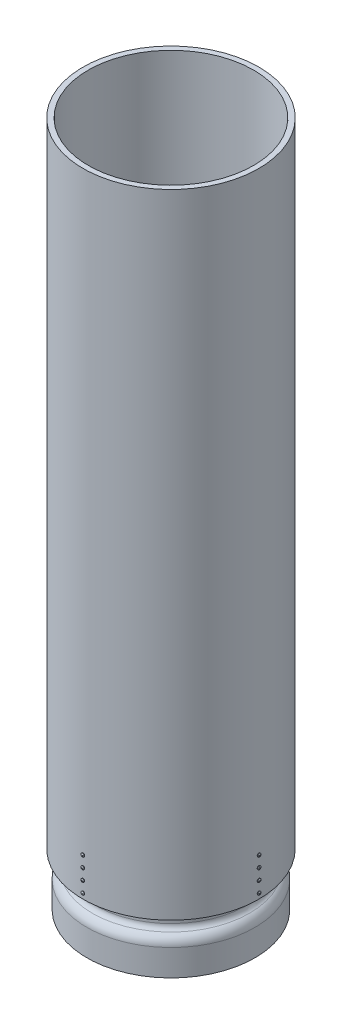
SolidWorks part; units mm, degrees
ref_plane "Front" through (0, 0, 0) normal (0, 0, 1) x (1, 0, 0)
ref_plane "Top" through (0, 0, 0) normal (0, 1, 0) x (1, 0, 0)
ref_plane "Right" through (0, 0, 0) normal (1, 0, 0) x (0, 0, -1)
sketch "Sketch2" plane through (0, 0, 0) normal (0, 0, 1) x (1, 0, 0)
  line L0 (0, -96.4651) -> (0, 112.46) construction
  line L1 (-228.6, 0) -> (-228.6, 76.2)
  line L2 (-238.9378, 152.4) -> (-238.9378, 1981.2)
  line L3 (-238.9378, 1981.2) -> (-254, 1981.2)
  line L4 (-254, 1981.2) -> (-254, 152.4)
  line L5 (-254, 152.4) -> (-238.9378, 152.4)
  line L6 (-228.6, 0) -> (-242.8748, 0)
  line L7 (-242.8748, 0) -> (-242.8748, 76.2)
  line L10 (0, 79.375) -> (0, 76.2)
  line L12 (-218.3003, 118.8009) -> (-218.3003, 279.4)
  line L13 (-218.3003, 279.4) -> (-204.0255, 279.4)
  line L14 (-204.0255, 279.4) -> (-204.0255, 118.8009)
  arc A0 (-227.0203, 103.6845) -> (-242.8748, 76.2) centre (-211.1248, 76.2) ccw
  arc A2 (-219.88, 91.3165) -> (-228.6, 76.2) centre (-211.1375, 76.2) ccw
  arc A3 (-219.88, 91.3165) -> (-204.0255, 118.8009) centre (-235.7755, 118.8009) ccw
  arc A4 (-227.0203, 103.6845) -> (-218.3003, 118.8009) centre (-235.7628, 118.8009) ccw
  dimension "D9" = 17.4625
  dimension "D10" = 76.2
  dimension "D8" = 31.75
  dimension "D13" = 31.75
  dimension "D14" = 17.4625
  dimension "D1" = 1981.2
  dimension "D2" = 14.2748
  dimension "D3" = 15.0622
  dimension "D4" = 508
  dimension "D5" = 457.2
  dimension "D6" = 152.4
  dimension "D7" = 14.2748
  dimension "D11" = 279.4
  dimension "D12" = 20.6375
revolve "Revolve1" add sketch "Sketch2" angle 360 about L0
sketch "Sketch3" plane through (0, 152.4, 0) normal (0, -1, 0) x (1, 0, 0)
  line L0 (-9.525, 238.7479) -> (-9.525, 218.0924)
  line L1 (9.525, 238.7479) -> (9.525, 218.0924)
  circle A0 centre (0, 0) radius 218.3003 construction
  arc A1 (9.525, 218.0924) -> (-9.525, 218.0924) centre (0, 0) ccw
  circle A2 centre (0, 0) radius 238.9378 construction
  arc A3 (9.525, 238.7479) -> (-9.525, 238.7479) centre (0, 0) ccw
  point P5 (0, 218.3003)
  dimension "D1" = 19.05
extrude "Boss-Extrude1" add sketch "Sketch3" against normal blind 127 separate body
ref_plane "Plane1" through (0, 0, 254) normal (0, 0, 1) x (1, 0, 0)
sketch "Sketch4" plane through (0, 0, 254) normal (0, 0, 1) x (1, 0, 0)
  line L0 (-9.525, 279.4) -> (-9.525, 152.4) construction
  line L1 (-9.525, 279.4) -> (-9.525, 152.4) construction
  line L2 (0, 200.025) -> (0, 231.775) construction
  line L3 (-9.525, 215.9) -> (0, 215.9) construction
  line L4 (0, 263.525) -> (0, 231.775) construction
  line L5 (0, 200.025) -> (0, 168.275) construction
  line L8 (0, 200.025) -> (18.0235, 200.025) construction
  line L9 (0, 215.9) -> (18.0235, 215.9) construction
  line L10 (18.0235, 215.9) -> (18.0235, 200.025) construction
  line L11 (0, 168.275) -> (0, 152.4) construction
  line L12 (-9.525, 152.4) -> (9.525, 152.4) construction
  line L13 (0, 263.525) -> (0, 279.4) construction
  line L14 (9.525, 279.4) -> (-9.525, 279.4) construction
  circle A0 centre (0, 168.275) radius 2.5527
  circle A1 centre (0, 200.025) radius 2.5527
  circle A2 centre (0, 231.775) radius 2.5527
  circle A3 centre (0, 263.525) radius 2.5527
  dimension "D1" = 5.1054
  dimension "D2" = 15.875
  dimension "D3" = 31.75
extrude "Cut-Extrude1" cut sketch "Sketch4" against normal blind 25.4
pattern_circular "CirPattern1" count 4 over 360 about axis through (0, 0, 0) along (0, 1, 0) of bodies 111 105
pattern_circular "CirPattern2" count 4 over 360 about axis through (0, 152.4, 0) along (0, -1, 0) of "Cut-Extrude1"
sketch "Sketch6" plane through (0, 0, 0) normal (1, 0, 0) x (0, 0, -1)
  line L0 (-277.6447, 263.525) -> (-230.3553, 263.525) construction
  line L1 (-254, 152.4) -> (254, 152.4) construction
  line L2 (-254, 263.525) -> (-254, 258.7879)
  line L3 (-254, 258.7879) -> (-255.5875, 258.7879)
  line L4 (-254, 263.525) -> (-257.3782, 263.525)
  line L5 (-254, 229.2223) -> (-254, 202.5777) construction
  arc A1 (-257.3782, 263.525) -> (-255.5875, 258.7879) centre (-250.2171, 263.525) ccw
  point P12 (-254, 261.1565)
  dimension "D1" = 111.125
  dimension "D2" = 3.3782
  dimension "D3" = 9.4742
  dimension "D4" = 1.5875
revolve "Revolve2" add sketch "Sketch6" angle 360 about L0
ref_plane "Plane2" through (0, 0, 257.3782) normal (0, 0, 1) x (1, 0, 0)
sketch "Sketch7" plane through (0, 0, 257.3782) normal (0, 0, 1) x (1, 0, 0)
  line L0 (-4.7371, 263.525) -> (-2.3813, 263.525) construction
  line L1 (2.3813, 263.9219) -> (0.3969, 263.9219)
  line L2 (2.3813, 263.9219) -> (2.3813, 263.1281)
  line L3 (2.3813, 263.1281) -> (0.3969, 263.1281)
  line L4 (-2.3813, 263.9219) -> (-2.3813, 263.1281)
  line L5 (0.3969, 265.9062) -> (-0.3969, 265.9062)
  line L6 (0.3969, 265.9062) -> (0.3969, 263.9219)
  line L7 (0.3969, 261.1438) -> (-0.3969, 261.1438)
  line L8 (-0.3969, 265.9062) -> (-0.3969, 263.9219)
  line L9 (0, 268.2621) -> (0, 265.9062) construction
  line L10 (0, 265.9062) -> (0, 261.1438) construction
  line L11 (-2.3813, 263.525) -> (2.3813, 263.525) construction
  line L12 (0, 261.1438) -> (0, 258.7879) construction
  line L13 (-0.3969, 263.1281) -> (-0.3969, 261.1438)
  line L14 (-0.3969, 263.1281) -> (-2.3813, 263.1281)
  line L15 (0.3969, 263.1281) -> (0.3969, 261.1438)
  line L16 (-0.3969, 263.9219) -> (-2.3813, 263.9219)
  circle A0 centre (0, 263.525) radius 4.7371 construction
  point P8 (0, 263.525)
  point P13 (0, 263.525)
  dimension "D1" = 0.7937
  dimension "D2" = 0.7937
  dimension "D3" = 4.7625
  dimension "D4" = 4.7625
extrude "Cut-Extrude2" cut sketch "Sketch7" against normal blind 1.5875
pattern_linear "LPattern1" count 4 spacing 31.75 along (0, -1, 0) of bodies 115
pattern_circular "CirPattern3" count 4 over 360 about axis through (0, 0, 0) along (0, 1, 0) of bodies 116 118 117 115
